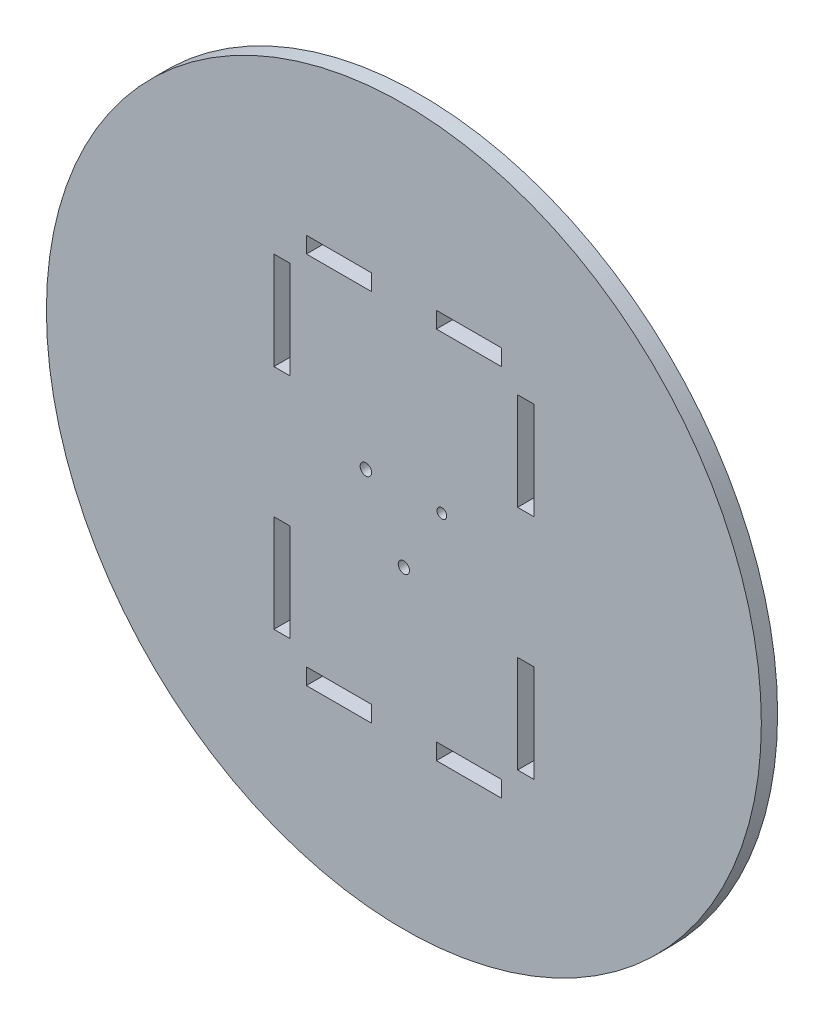
SolidWorks part; units mm, degrees
ref_plane "Front Plane" through (0, 0, 0) normal (0, 0, 1) x (1, 0, 0)
ref_plane "Top Plane" through (0, 0, 0) normal (0, 1, 0) x (1, 0, 0)
ref_plane "Right Plane" through (0, 0, 0) normal (1, 0, 0) x (0, 0, -1)
sketch "Sketch1" plane through (0, 0, 0) normal (0, 0, 1) x (1, 0, 0)
  line L0 (-40, 60) -> (40, 60) construction
  line L1 (40, 60) -> (40, -60) construction
  line L2 (40, -60) -> (-40, -60) construction
  line L3 (-40, -60) -> (-40, 60) construction
  line L4 (-11.6913, 6.75) -> (0, 0) construction
  line L5 (-30, 60) -> (-10, 60)
  line L6 (-30, 60) -> (-30, 55)
  line L7 (-30, 55) -> (-10, 55)
  line L8 (-10, 60) -> (-10, 55)
  line L9 (10, 60) -> (30, 60)
  line L10 (10, 60) -> (10, 55)
  line L11 (10, 55) -> (30, 55)
  line L12 (30, 60) -> (30, 55)
  line L13 (40, 50) -> (35, 50)
  line L14 (40, 50) -> (40, 20)
  line L15 (40, 20) -> (35, 20)
  line L16 (35, 50) -> (35, 20)
  line L17 (40, -20) -> (35, -20)
  line L18 (40, -20) -> (40, -50)
  line L19 (40, -50) -> (35, -50)
  line L20 (35, -20) -> (35, -50)
  line L21 (30, -60) -> (10, -60)
  line L22 (30, -60) -> (30, -55)
  line L23 (30, -55) -> (10, -55)
  line L24 (10, -60) -> (10, -55)
  line L25 (-10, -60) -> (-30, -60)
  line L26 (-10, -60) -> (-10, -55)
  line L27 (-10, -55) -> (-30, -55)
  line L28 (-30, -60) -> (-30, -55)
  line L29 (-40, -50) -> (-35, -50)
  line L30 (-40, -50) -> (-40, -20)
  line L31 (-40, -20) -> (-35, -20)
  line L32 (-35, -50) -> (-35, -20)
  line L33 (-40, 20) -> (-35, 20)
  line L34 (-40, 20) -> (-40, 50)
  line L35 (-40, 50) -> (-35, 50)
  line L36 (-35, 20) -> (-35, 50)
  line L37 (0, 0) -> (11.6913, 6.75) construction
  line L38 (0, 0) -> (0, -13.5) construction
  circle A0 centre (0, 0) radius 110
  circle A2 centre (-11.6913, 6.75) radius 1.7689
  circle A3 centre (11.6913, 6.75) radius 1.4939
  circle A4 centre (0, -13.5) radius 1.7392
  point P6 (0, -60)
  dimension "D1" = 220
  dimension "D31" = 120
  dimension "D2" = 80
  dimension "D3" = 120
  dimension "D4" = 40
  dimension "D5" = 60
  dimension "D6" = 10
  dimension "D7" = 20
  dimension "D8" = 20
  dimension "D9" = 20
  dimension "D10" = 10
  dimension "D11" = 30
  dimension "D12" = 40
  dimension "D13" = 30
  dimension "D14" = 10
  dimension "D15" = 20
  dimension "D16" = 20
  dimension "D17" = 20
  dimension "D18" = 10
  dimension "D19" = 30
  dimension "D20" = 40
  dimension "D21" = 30
  dimension "D22" = 5
  dimension "D23" = 5
  dimension "D24" = 5
  dimension "D25" = 5
  dimension "D26" = 5
  dimension "D27" = 5
  dimension "D28" = 5
  dimension "D29" = 5
  dimension "D32" = 120
extrude "Boss-Extrude1" add sketch "Sketch1" along normal blind 5
